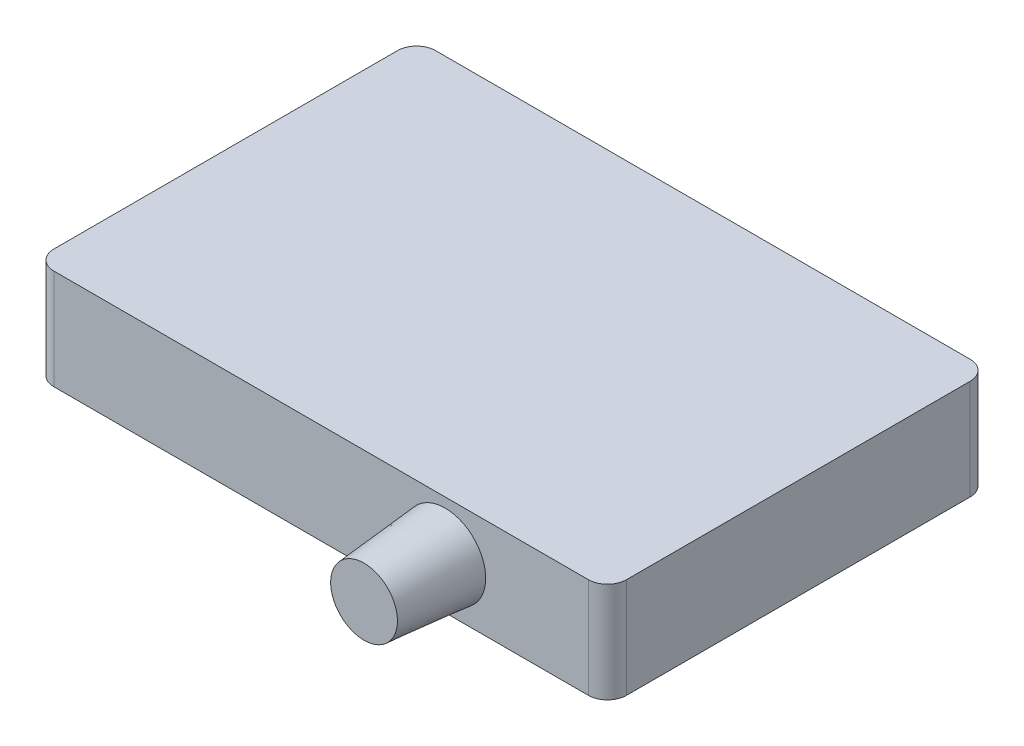
SolidWorks part; units mm, degrees
ref_plane "前视基准面" through (0, 0, 0) normal (0, 0, 1) x (1, 0, 0)
ref_plane "上视基准面" through (0, 0, 0) normal (0, 1, 0) x (1, 0, 0)
ref_plane "右视基准面" through (0, 0, 0) normal (1, 0, 0) x (0, 0, -1)
sketch "草图1" plane through (0, 0, 0) normal (0, 1, 0) x (1, 0, 0)
  line L1 (-28, 20) -> (28, 20)
  line L2 (-30, 18) -> (-30, -18)
  line L3 (-28, -20) -> (28, -20)
  line L4 (30, 18) -> (30, -18)
  line L5 (-30, 20) -> (30, -20) construction
  line L6 (-30, -20) -> (30, 20) construction
  arc A0 (28, -20) -> (30, -18) centre (28, -18) ccw
  arc A1 (-28, -20) -> (-30, -18) centre (-28, -18) cw
  arc A2 (30, 18) -> (28, 20) centre (28, 18) ccw
  arc A3 (-28, 20) -> (-30, 18) centre (-28, 18) ccw
  point P0 (0, 0)
  dimension "D3" = 2
  dimension "D1" = 60
  dimension "D2" = 40
extrude "凸台-拉伸1" add sketch "草图1" along normal blind 10.5
sketch "草图2" plane through (0, 0, -20) normal (0, 0, -1) x (-1, 0, 0)
  line L0 (-28, 4) -> (-18, 4) construction
  line L1 (-28, 10.5) -> (-28, 0) construction
  line L2 (-28, 0) -> (28, 0) construction
  circle A0 centre (-18, 4) radius 2.25
  circle A1 centre (-12, 4) radius 2.25
  circle A2 centre (-6, 4) radius 2.25
  dimension "D3" = 4.5
  dimension "D1" = 4
  dimension "D2" = 10
  dimension "D4" = 3
extrude "切除-拉伸1" cut sketch "草图2" against normal blind 4
sketch "草图3" plane through (0, 0, -20) normal (0, 0, -1) x (-1, 0, 0)
  circle A0 centre (-18, 4) radius 2.25 construction
  circle A1 centre (-18, 4) radius 2.25
  circle A2 centre (-18, 4) radius 2.75
  circle A3 centre (-12, 4) radius 2.75
  circle A4 centre (-12, 4) radius 2.25
  circle A5 centre (-6, 4) radius 2.75
  circle A6 centre (-6, 4) radius 2.25
  dimension "D1" = 0.5
  dimension "D2" = 3
extrude "凸台-拉伸2" add sketch "草图3" along normal blind 0.5
chamfer "倒角1" distance 0.25 angle 45 3 edges at (3.25, 4, -20.5) (9.25, 4, -20.5) (15.25, 4, -20.5)
sketch "草图4" plane through (0, 0, 20) normal (0, 0, 1) x (1, 0, 0)
  line L0 (28, 5.25) -> (13, 5.25) construction
  line L1 (28, 10.5) -> (28, 0) construction
  circle A0 centre (13, 5.25) radius 3.5
  dimension "D2" = 7
  dimension "D1" = 15
extrude "凸台-拉伸3" add sketch "草图4" along normal blind 8.5
draft "拔模1" type of draft neutral plane draft angle 5 faces to draft 1 face at (16.5, 5.25, 28.5) neutral plane through (13, 5.25, 28.5) neutral plane normal (0, 0, 1) parameters "D1"=5
